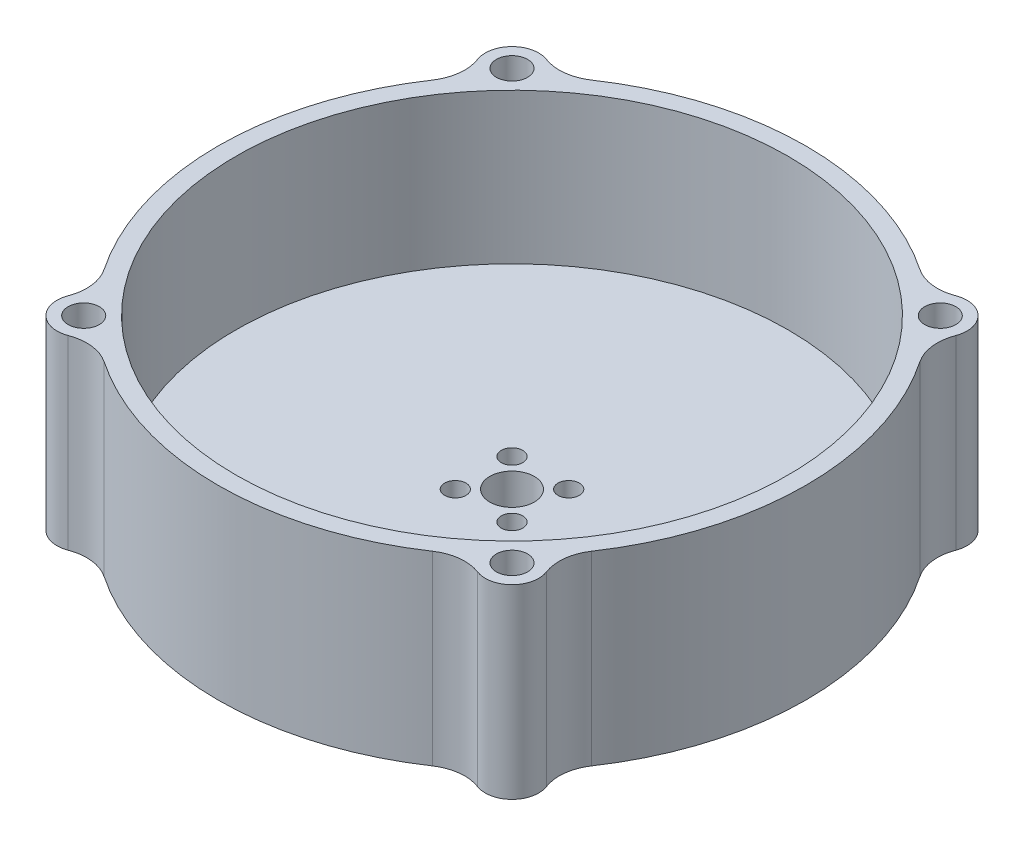
SolidWorks part; units mm, degrees
ref_plane "Front Plane" through (0, 0, 0) normal (0, 0, 1) x (1, 0, 0)
ref_plane "Top Plane" through (0, 0, 0) normal (0, 1, 0) x (1, 0, 0)
ref_plane "Right Plane" through (0, 0, 0) normal (1, 0, 0) x (0, 0, -1)
sketch "Sketch1" plane through (0, 0, 0) normal (0, 1, 0) x (1, 0, 0)
  circle A0 centre (0, 0) radius 33
  dimension "D1" = 66
extrude "Boss-Extrude1" add sketch "Sketch1" along normal blind 4
sketch "Sketch2" plane through (0, 4, 0) normal (0, 1, 0) x (1, 0, 0)
  circle A0 centre (0, 0) radius 31
  circle A1 centre (0, 0) radius 33 construction
  circle A2 centre (0, 0) radius 33
  dimension "D1" = 62
extrude "Boss-Extrude2" add sketch "Sketch2" along normal blind 16.88
sketch "Sketch5" plane through (0, 0, 0) normal (0, -1, 0) x (1, 0, 0)
  line L1 (-3.182, 3.182) -> (3.182, 3.182)
  line L2 (-3.182, 3.182) -> (-3.182, -3.182)
  line L3 (-3.182, -3.182) -> (3.182, -3.182)
  line L4 (3.182, 3.182) -> (3.182, -3.182)
  circle A0 centre (0, 0) radius 4.5
  dimension "D1" = 9
hole_wizard "M2 Clearance Hole1" positions "Sketch6" profile "Sketch8" hole size "M2" standard "ANSI Metric" end condition through all
sketch "Sketch6" plane through (0, 0, 0) normal (0, -1, 0) x (-1, 0, 0)
  point P0 (3.182, 3.182)
  point P3 (3.182, -3.182)
  point P6 (-3.182, -3.182)
  point P9 (-3.182, 3.182)
sketch "Sketch8" plane through (-3.182, 0, -3.182) normal (1, 0, 0) x (0, 0, -1)
  line L0 (0, 0) -> (0, 20.88)
  line L1 (0, 20.88) -> (1.2, 20.88)
  line L2 (1.2, 20.88) -> (1.2, 0)
  line L5 (1.2, 0) -> (0, 0)
  line L11 (0, -6.35) -> (0, 107.95) construction
  dimension "Thru Hole Dia." = 2.4
  dimension "Thru Hole Depth" = 20.88
sketch "Sketch13" plane through (0, 4, 0) normal (0, 1, 0) x (1, 0, 0)
  circle A0 centre (0, 0) radius 2.5
  dimension "D1" = 5
extrude "Cut-Extrude3" cut sketch "Sketch13" against normal through all
sketch "Sketch10" plane through (0, 4, 0) normal (0, 1, 0) x (1, 0, 0)
  line L0 (15, -4) -> (15, 4) construction
  line L1 (13.5, -4) -> (13.5, 4)
  line L2 (16.5, -4) -> (16.5, 4)
  arc A1 (13.5, -4) -> (16.5, -4) centre (15, -4) ccw
  arc A2 (16.5, 4) -> (13.5, 4) centre (15, 4) ccw
  point P2 (15, 0)
  dimension "D1" = 15
  dimension "D2" = 8
  dimension "D3" = 3
extrude "Cut-Extrude2" cut sketch "Sketch10" against normal through all
sketch "Sketch15" plane through (0, 20.88, 0) normal (0, 1, 0) x (1, 0, 0)
  line L0 (0, 0) -> (24.0416, 24.0416) construction
  line L1 (13.5, 4) -> (13.5, -4) construction
  circle A0 centre (24.0416, 24.0416) radius 3
  circle A1 centre (0, 0) radius 31 construction
  dimension "D1" = 6
  dimension "D2" = 45
extrude "Boss-Extrude3" add sketch "Sketch15" against normal through all
fillet "Fillet1" radius 5 2 edges at (25.2199, 10.44, -21.2827) (21.2827, 10.44, -25.2199)
pattern_circular "CirPattern1" count 4 over 360 about axis through (0, 0, 0) along (0, 1, 0) of "Boss-Extrude3", "Fillet1"
hole_wizard "Ø3.0 mm Dowel Holes1" positions "Sketch18" profile "Sketch19" hole size "Ø3.0" standard "ANSI Metric" end condition through all
sketch "Sketch18" plane through (0, 20.88, 0) normal (0, 1, 0) x (1, 0, 0)
  point P5 (24.0416, -24.0416)
  point P8 (-24.0416, -24.0416)
  point P14 (-24.0416, 24.0416)
  point P17 (24.0416, 24.0416)
sketch "Sketch19" plane through (24.0416, 20.88, 24.0416) normal (1, 0, 0) x (0, 0, 1)
  line L0 (0, 0) -> (0, 20.88)
  line L1 (0, 20.88) -> (1.75, 20.88)
  line L2 (1.75, 20.88) -> (1.75, 0)
  line L5 (1.75, 0) -> (0, 0)
  line L11 (0, -6.35) -> (0, 107.95) construction
  dimension "Thru Hole Dia." = 3.5
  dimension "Thru Hole Depth" = 20.88
